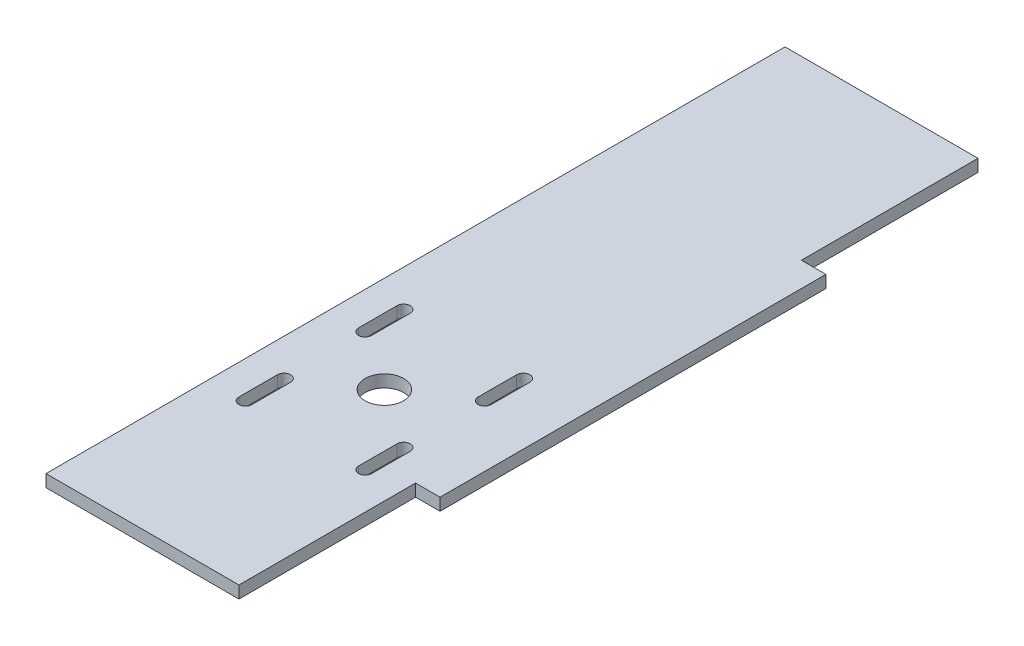
SolidWorks part; units mm, degrees
ref_plane "Front Plane" through (0, 0, 0) normal (0, 0, 1) x (1, 0, 0)
ref_plane "Top Plane" through (0, 0, 0) normal (0, 1, 0) x (1, 0, 0)
ref_plane "Right Plane" through (0, 0, 0) normal (1, 0, 0) x (0, 0, -1)
sketch "Sketch1" plane through (0, 0, 0) normal (0, 1, 0) x (1, 0, 0)
  line L0 (-25, 45.75) -> (25, 45.75)
  line L1 (25, 45.75) -> (25, 0)
  line L2 (25, 0) -> (31.35, 0)
  line L3 (31.35, 0) -> (31.35, -100)
  line L4 (31.35, -100) -> (25, -100)
  line L5 (25, -100) -> (25, -145.75)
  line L6 (25, -145.75) -> (-25, -145.75)
  line L7 (-25, -145.75) -> (-25, -100)
  line L8 (-25, -100) -> (-31.35, -100)
  line L9 (-31.35, -100) -> (-31.35, 0)
  line L10 (-31.35, 0) -> (-25, 0)
  line L11 (-25, 0) -> (-25, 45.75)
  line L12 (-25, 0) -> (-25, -100) construction
  point P11 (0, 45.75)
  point P14 (-31.35, -50)
  dimension "D1" = 6.35
  dimension "D2" = 100
  dimension "D3" = 50
  dimension "D4" = 191.5
extrude "Boss-Extrude1" add sketch "Sketch1" along normal blind 3.175 contours L11 L12 L7 L6 L5 L4 L3 L2 L1 L0
sketch "Sketch3" plane through (0, 3.175, 0) normal (0, 1, 0) x (1, 0, 0)
  line L1 (21.25, -104.325) -> (-21.25, -104.325) construction
  line L2 (21.25, -104.325) -> (21.25, -61.825) construction
  line L3 (21.25, -61.825) -> (-21.25, -61.825) construction
  line L4 (-21.25, -104.325) -> (-21.25, -61.825) construction
  line L5 (21.25, -104.325) -> (-21.25, -61.825) construction
  line L6 (21.25, -61.825) -> (-21.25, -104.325) construction
  line L7 (0, -58.575) -> (0, -107.575) construction
  line L8 (-25, 45.75) -> (25, 45.75) construction
  circle A0 centre (0, -83.075) radius 5
  point P0 (0, -83.075)
  point P5 (0, -62.25)
  point P13 (15.5, -98.575)
  point P14 (-15.5, -98.575)
  point P15 (-15.5, -67.575)
  point P16 (15.5, -67.575)
  dimension "D4" = 10
  dimension "D5" = 49
  dimension "D3" = 42.5
  dimension "D6" = 31
  dimension "D1" = 128.825
extrude "Cut-Extrude1" cut sketch "Sketch3" against normal through all
hole_wizard "M3 Clearance Hole1" positions "Sketch5" profile "Sketch4" hole size "M3" standard "ANSI Metric" end condition through all
sketch "Sketch5" plane through (0, 3.175, 0) normal (0, 1, 0) x (1, 0, 0)
  point P6 (15.5, -98.575)
  point P9 (-15.5, -98.575)
  point P12 (-15.5, -67.575)
  point P15 (15.5, -67.575)
sketch "Sketch4" plane through (15.5, 3.175, 98.575) normal (1, 0, 0) x (0, 0, 1)
  line L0 (0, 0) -> (0, 3.175)
  line L1 (0, 3.175) -> (1.7, 3.175)
  line L2 (1.7, 3.175) -> (1.7, 0)
  line L5 (1.7, 0) -> (0, 0)
  line L11 (0, -6.35) -> (0, 107.95) construction
  dimension "Thru Hole Dia." = 3.4
  dimension "Thru Hole Depth" = 3.175
sketch "Sketch6" plane through (0, 0, 0) normal (0, -1, 0) x (1, 0, 0)
  line L0 (15.5, 103.575) -> (15.5, 93.575) construction
  line L1 (17.2, 103.575) -> (17.2, 93.575)
  line L2 (13.8, 103.575) -> (13.8, 93.575)
  line L3 (-15.5, 103.575) -> (-15.5, 93.575) construction
  line L4 (-13.8, 103.575) -> (-13.8, 93.575)
  line L5 (-17.2, 103.575) -> (-17.2, 93.575)
  line L6 (20.4495, 83.075) -> (-20.4495, 83.075) construction
  line L7 (15.5, 62.575) -> (15.5, 72.575) construction
  line L8 (17.2, 62.575) -> (17.2, 72.575)
  line L9 (13.8, 62.575) -> (13.8, 72.575)
  line L10 (-15.5, 62.575) -> (-15.5, 72.575) construction
  line L11 (-13.8, 62.575) -> (-13.8, 72.575)
  line L12 (-17.2, 62.575) -> (-17.2, 72.575)
  arc A0 (17.2, 103.575) -> (13.8, 103.575) centre (15.5, 103.575) ccw
  arc A1 (13.8, 93.575) -> (17.2, 93.575) centre (15.5, 93.575) ccw
  arc A2 (-13.8, 103.575) -> (-17.2, 103.575) centre (-15.5, 103.575) ccw
  arc A3 (-17.2, 93.575) -> (-13.8, 93.575) centre (-15.5, 93.575) ccw
  circle A5 centre (0, 83.075) radius 5 construction
  circle A6 centre (-15.5, 98.575) radius 1.7 construction
  circle A7 centre (15.5, 98.575) radius 1.7 construction
  arc A8 (17.2, 62.575) -> (13.8, 62.575) centre (15.5, 62.575) cw
  arc A9 (13.8, 72.575) -> (17.2, 72.575) centre (15.5, 72.575) cw
  arc A10 (-13.8, 62.575) -> (-17.2, 62.575) centre (-15.5, 62.575) cw
  arc A11 (-17.2, 72.575) -> (-13.8, 72.575) centre (-15.5, 72.575) cw
  point P2 (15.5, 98.575)
  point P10 (-15.5, 98.575)
  point P20 (0, 83.075)
  point P27 (15.5, 67.575)
  point P34 (-15.5, 67.575)
  dimension "D1" = 10
extrude "Cut-Extrude2" cut sketch "Sketch6" against normal through all
equation "\"length\"= 191.5mm"
equation "\"w_mach\"= 50mm"
equation "\"w_tab\"= 100mm"
equation "\"t_wood\"= 0.125in"
equation "\"t_side\"= 0.25in"
equation "\"D1@Sketch1\"=\"t_side\""
equation "\"D2@Sketch1\"=\"w_tab\""
equation "\"D3@Sketch1\"=\"w_mach\""
equation "\"D4@Sketch1\"=\"length\""
equation "\"D1@Boss-Extrude1\"=\"t_wood\""
equation "\"l_motor\"= 42.5mm"
equation "\"l_servo\"= 0"
equation "\"servocenter\"= 6.35mm"
equation "\"servoholes\"= 49mm"
equation "\"dY\"= 144.825mm"
equation "\"in_rad\"= 16mm"
equation "\"D1@Sketch3\"= \"dY\" - \"in_rad\""
equation "\"D5@Sketch3\"= \"servoholes\""
equation "\"D3@Sketch3\"=\"l_motor\""
